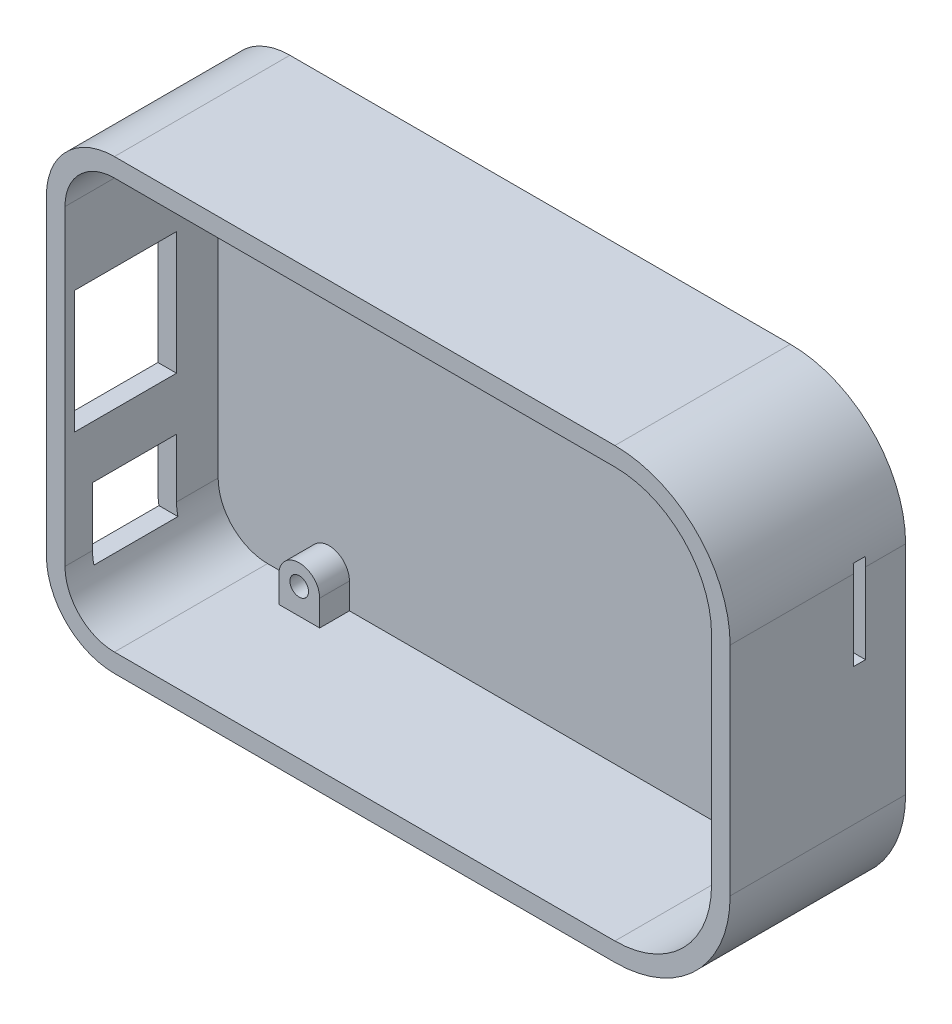
SolidWorks part; units mm, degrees
ref_plane "Front Plane" through (0, 0, 0) normal (0, 0, 1) x (1, 0, 0)
ref_plane "Top Plane" through (0, 0, 0) normal (0, 1, 0) x (1, 0, 0)
ref_plane "Right Plane" through (0, 0, 0) normal (1, 0, 0) x (0, 0, -1)
sketch "BeagleBone board" plane through (0, 0, 0) normal (0, 0, 1) x (1, 0, 0)
  line L1 (6.35, 0) -> (73.66, 0)
  line L2 (0, 6.35) -> (0, 48.26)
  line L3 (6.35, 54.61) -> (73.66, 54.61)
  line L4 (86.36, 12.7) -> (86.36, 41.91)
  line L5 (-2.5, 5) -> (12, 5)
  line L6 (-2.5, 5) -> (-2.5, 14)
  line L7 (-2.5, 14) -> (12, 14)
  line L8 (12, 5) -> (12, 14)
  line L9 (-2.5, 21.6) -> (19, 21.6)
  line L10 (-2.5, 21.6) -> (-2.5, 37.6)
  line L11 (-2.5, 37.6) -> (19, 37.6)
  line L12 (19, 21.6) -> (19, 37.6)
  arc A0 (6.35, 0) -> (0, 6.35) centre (6.35, 6.35) cw
  arc A1 (0, 48.26) -> (6.35, 54.61) centre (6.35, 48.26) cw
  arc A2 (73.66, 0) -> (86.36, 12.7) centre (73.66, 12.7) ccw
  arc A3 (73.66, 54.61) -> (86.36, 41.91) centre (73.66, 41.91) cw
  circle A4 centre (14.605, 51.435) radius 1.5
  circle A5 centre (14.605, 3.175) radius 1.5
  circle A6 centre (80.645, 48.26) radius 1.5
  circle A7 centre (80.645, 6.35) radius 1.5
  point P7 (0, 0)
  dimension "D3" = 6.35
  dimension "D4" = 12.7
  dimension "D5" = 3
  dimension "D1" = 86.36
  dimension "D2" = 54.61
  dimension "D6" = 3.175
  dimension "D7" = 14.605
  dimension "D8" = 51.435
  dimension "D9" = 6.35
  dimension "D10" = 48.26
  dimension "D11" = 80.645
  dimension "D12" = 2.5
  dimension "D13" = 16
  dimension "D14" = 21.5
  dimension "D15" = 9
  dimension "D16" = 14.5
  dimension "D17" = 5
  dimension "D18" = 21.6
sketch "Sketch5" plane through (0, 0, 0) normal (0, 0, 1) x (1, 0, 0)
  line L4 (73.66, 57.41) -> (6.35, 57.41)
  line L5 (-2.8, 48.26) -> (-2.8, 6.35)
  line L6 (6.35, -2.8) -> (73.66, -2.8)
  line L7 (89.16, 12.7) -> (89.16, 41.91)
  line L8 (73.66, 54.91) -> (6.35, 54.91)
  line L9 (86.66, 12.7) -> (86.66, 41.91)
  line L10 (6.35, -0.3) -> (73.66, -0.3)
  line L11 (-0.3, 48.26) -> (-0.3, 6.35)
  line L12 (73.66, 54.91) -> (17.355, 54.91)
  line L13 (86.66, 12.7) -> (86.66, 41.91)
  line L14 (6.35, -0.3) -> (11.855, -0.3)
  line L15 (-0.3, 48.26) -> (-0.3, 6.35)
  line L16 (17.355, 51.435) -> (17.355, 54.91)
  line L17 (11.855, 51.435) -> (11.855, 54.91)
  line L18 (77.895, 48.26) -> (77.895, 54.2008)
  line L19 (80.645, 45.51) -> (86.1516, 45.51)
  line L20 (77.895, 6.35) -> (77.895, 0.4092)
  line L21 (80.645, 9.1) -> (86.1516, 9.1)
  line L22 (11.855, 3.175) -> (11.855, -0.3)
  line L23 (17.355, -0.3) -> (73.66, -0.3)
  line L24 (6.35, -0.3) -> (73.66, -0.3) construction
  line L25 (17.355, 3.175) -> (17.355, -0.3)
  line L26 (11.855, 54.91) -> (6.35, 54.91)
  line L27 (73.66, 54.91) -> (6.35, 54.91) construction
  arc A4 (6.35, 57.41) -> (-2.8, 48.26) centre (6.35, 48.26) ccw
  arc A5 (-2.8, 6.35) -> (6.35, -2.8) centre (6.35, 6.35) ccw
  arc A6 (73.66, -2.8) -> (89.16, 12.7) centre (73.66, 12.7) ccw
  arc A7 (89.16, 41.91) -> (73.66, 57.41) centre (73.66, 41.91) ccw
  arc A8 (86.66, 41.91) -> (73.66, 54.91) centre (73.66, 41.91) ccw
  arc A9 (73.66, -0.3) -> (86.66, 12.7) centre (73.66, 12.7) ccw
  arc A10 (-0.3, 6.35) -> (6.35, -0.3) centre (6.35, 6.35) ccw
  arc A11 (6.35, 54.91) -> (-0.3, 48.26) centre (6.35, 48.26) ccw
  arc A12 (86.66, 41.91) -> (86.1516, 45.51) centre (73.66, 41.91) ccw
  arc A13 (73.66, -0.3) -> (77.895, 0.4092) centre (73.66, 12.7) ccw
  arc A14 (-0.3, 6.35) -> (6.35, -0.3) centre (6.35, 6.35) ccw
  arc A15 (6.35, 54.91) -> (-0.3, 48.26) centre (6.35, 48.26) ccw
  circle A16 centre (14.605, 51.435) radius 1.25
  arc A17 (11.855, 51.435) -> (17.355, 51.435) centre (14.605, 51.435) ccw
  circle A18 centre (80.645, 48.26) radius 1.25
  arc A19 (77.895, 48.26) -> (80.645, 45.51) centre (80.645, 48.26) ccw
  circle A20 centre (80.645, 6.35) radius 1.25
  arc A21 (80.645, 9.1) -> (77.895, 6.35) centre (80.645, 6.35) ccw
  circle A22 centre (14.605, 3.175) radius 1.25
  arc A23 (17.355, 3.175) -> (11.855, 3.175) centre (14.605, 3.175) ccw
  arc A24 (86.1516, 9.1) -> (86.66, 12.7) centre (73.66, 12.7) ccw
  arc A25 (73.66, -0.3) -> (86.66, 12.7) centre (73.66, 12.7) ccw construction
  arc A26 (77.895, 54.2008) -> (73.66, 54.91) centre (73.66, 41.91) ccw
  arc A27 (86.66, 41.91) -> (73.66, 54.91) centre (73.66, 41.91) ccw construction
  dimension "D3" = 2.5
  dimension "D4" = 5.5
  dimension "D1" = 0.3
  dimension "D2" = 2.5
extrude "Bottom frame" add sketch "Sketch5" along normal blind 4
sketch "Sketch6" plane through (0, 0, 4) normal (0, 0, 1) x (1, 0, 0)
  line L0 (-0.3, 48.26) -> (-0.3, 6.35) construction
  line L1 (-0.3, 48.26) -> (-0.3, 6.35)
  line L2 (86.66, 41.91) -> (86.66, 12.7)
  line L3 (73.66, 54.91) -> (6.35, 54.91)
  line L4 (73.66, 57.41) -> (6.35, 57.41)
  line L5 (-2.8, 48.26) -> (-2.8, 6.35)
  line L6 (6.35, -2.8) -> (73.66, -2.8)
  line L7 (89.16, 12.7) -> (89.16, 41.91)
  line L8 (73.66, 57.41) -> (6.35, 57.41)
  line L9 (-2.8, 48.26) -> (-2.8, 6.35)
  line L10 (6.35, -2.8) -> (73.66, -2.8)
  line L11 (89.16, 12.7) -> (89.16, 41.91)
  line L12 (6.35, -0.3) -> (73.66, -0.3)
  arc A0 (6.35, 54.91) -> (-0.3, 48.26) centre (6.35, 48.26) ccw construction
  arc A1 (-0.3, 6.35) -> (6.35, -0.3) centre (6.35, 6.35) ccw construction
  arc A2 (6.35, 54.91) -> (-0.3, 48.26) centre (6.35, 48.26) ccw
  arc A3 (-0.3, 6.35) -> (6.35, -0.3) centre (6.35, 6.35) ccw
  arc A4 (89.16, 41.91) -> (73.66, 57.41) centre (73.66, 41.91) ccw
  arc A5 (6.35, 57.41) -> (-2.8, 48.26) centre (6.35, 48.26) ccw
  arc A6 (-2.8, 6.35) -> (6.35, -2.8) centre (6.35, 6.35) ccw
  arc A7 (73.66, -2.8) -> (89.16, 12.7) centre (73.66, 12.7) ccw
  arc A8 (89.16, 41.91) -> (73.66, 57.41) centre (73.66, 41.91) ccw
  arc A9 (6.35, 57.41) -> (-2.8, 48.26) centre (6.35, 48.26) ccw
  arc A10 (-2.8, 6.35) -> (6.35, -2.8) centre (6.35, 6.35) ccw
  arc A11 (73.66, -2.8) -> (89.16, 12.7) centre (73.66, 12.7) ccw
  arc A12 (86.66, 41.91) -> (73.66, 54.91) centre (73.66, 41.91) ccw
  arc A13 (77.895, 54.2008) -> (73.66, 54.91) centre (73.66, 41.91) ccw construction
  arc A14 (73.66, -0.3) -> (86.66, 12.7) centre (73.66, 12.7) ccw
  arc A15 (86.1516, 9.1) -> (86.66, 12.7) centre (73.66, 12.7) ccw construction
  dimension "D1" = 0
extrude "PCB" add sketch "Sketch6" along normal blind 1.6
sketch "Sketch7" plane through (0, 0, 5.6) normal (0, 0, 1) x (1, 0, 0)
  line L0 (73.66, 54.91) -> (6.35, 54.91) construction
  line L1 (73.66, 54.91) -> (6.35, 54.91)
  line L2 (-0.3, 48.26) -> (-0.3, 6.35) construction
  line L3 (-0.3, 48.26) -> (-0.3, 37.85)
  line L4 (73.66, 57.41) -> (6.35, 57.41)
  line L5 (-2.8, 48.26) -> (-2.8, 6.35)
  line L6 (6.35, -2.8) -> (73.66, -2.8)
  line L7 (89.16, 12.7) -> (89.16, 41.91)
  line L8 (73.66, 57.41) -> (6.35, 57.41)
  line L9 (-2.8, 48.26) -> (-2.8, 37.85)
  line L10 (6.35, -2.8) -> (73.66, -2.8)
  line L11 (89.16, 12.7) -> (89.16, 41.91)
  line L12 (6.35, -0.3) -> (73.66, -0.3) construction
  line L13 (6.35, -0.3) -> (73.66, -0.3)
  line L14 (86.66, 12.7) -> (86.66, 41.91) construction
  line L15 (86.66, 12.7) -> (86.66, 41.91)
  line L16 (-0.3, 21.35) -> (-2.8, 21.35)
  line L17 (-2.8, 37.85) -> (-0.3, 37.85)
  line L18 (-0.3, 21.35) -> (-0.3, 14.25)
  line L19 (-2.8, 21.35) -> (-2.8, 14.25)
  line L20 (-2.5, 21.6) -> (19, 21.6) construction
  line L21 (-2.5, 37.6) -> (19, 37.6) construction
  line L22 (-2.659, 4.75) -> (-0.1046, 4.75)
  line L23 (-0.3, 14.25) -> (-2.8, 14.25)
  line L24 (-2.5, 5) -> (12, 5) construction
  line L25 (-2.5, 14) -> (12, 14) construction
  arc A0 (6.35, 54.61) -> (0, 48.26) centre (6.35, 48.26) ccw construction
  arc A1 (6.35, 54.61) -> (0, 48.26) centre (6.35, 48.26) ccw
  arc A2 (6.35, 54.91) -> (-0.3, 48.26) centre (6.35, 48.26) ccw construction
  arc A3 (6.35, 54.91) -> (-0.3, 48.26) centre (6.35, 48.26) ccw
  arc A4 (89.16, 41.91) -> (73.66, 57.41) centre (73.66, 41.91) ccw
  arc A5 (6.35, 57.41) -> (-2.8, 48.26) centre (6.35, 48.26) ccw
  arc A6 (-2.8, 6.35) -> (6.35, -2.8) centre (6.35, 6.35) ccw
  arc A7 (73.66, -2.8) -> (89.16, 12.7) centre (73.66, 12.7) ccw
  arc A8 (89.16, 41.91) -> (73.66, 57.41) centre (73.66, 41.91) ccw
  arc A9 (6.35, 57.41) -> (-2.8, 48.26) centre (6.35, 48.26) ccw
  arc A10 (-2.659, 4.75) -> (6.35, -2.8) centre (6.35, 6.35) ccw
  arc A11 (73.66, -2.8) -> (89.16, 12.7) centre (73.66, 12.7) ccw
  arc A12 (-0.3, 6.35) -> (6.35, -0.3) centre (6.35, 6.35) ccw construction
  arc A13 (-0.1046, 4.75) -> (6.35, -0.3) centre (6.35, 6.35) ccw
  arc A14 (73.66, -0.3) -> (86.66, 12.7) centre (73.66, 12.7) ccw construction
  arc A15 (73.66, -0.3) -> (86.66, 12.7) centre (73.66, 12.7) ccw
  arc A16 (86.66, 41.91) -> (73.66, 54.91) centre (73.66, 41.91) ccw construction
  arc A17 (86.66, 41.91) -> (73.66, 54.91) centre (73.66, 41.91) ccw
  arc M9 (89.16, 41.91) -> (73.66, 57.41) centre (73.66, 41.91) ccw
  line M10 (73.66, 57.41) -> (6.35, 57.41)
  arc M11 (6.35, 57.41) -> (-2.8, 48.26) centre (6.35, 48.26) ccw
  line M12 (-2.8, 48.26) -> (-2.8, 6.35)
  arc M13 (-2.8, 6.35) -> (6.35, -2.8) centre (6.35, 6.35) ccw
  line M14 (6.35, -2.8) -> (73.66, -2.8)
  arc M15 (73.66, -2.8) -> (89.16, 12.7) centre (73.66, 12.7) ccw
  line M16 (89.16, 12.7) -> (89.16, 41.91)
  line M17 (6.35, 54.91) -> (73.66, 54.91)
  arc M18 (73.66, 54.91) -> (86.66, 41.91) centre (73.66, 41.91) cw
  line M19 (86.66, 41.91) -> (86.66, 12.7)
  arc M20 (86.66, 12.7) -> (73.66, -0.3) centre (73.66, 12.7) cw
  line M21 (73.66, -0.3) -> (6.35, -0.3)
  arc M22 (6.35, -0.3) -> (-0.3, 6.35) centre (6.35, 6.35) cw
  line M23 (-0.3, 6.35) -> (-0.3, 48.26)
  arc M24 (-0.3, 48.26) -> (6.35, 54.91) centre (6.35, 48.26) cw
  dimension "D2" = 0.25
  dimension "D3" = 0.25
  dimension "D4" = 0.25
  dimension "D5" = 0.25
  dimension "D1" = 0
extrude "upper frame" add sketch "Sketch7" along normal blind 15 contours L22 L17 M13 M14 M15 M16 M9 M10 M11 M12 M23 M24 M17 M18 M19 M20 M21 M22 | L23 L16 M23 M12
sketch "Sketch8" plane through (0, 0, 0) normal (0, 0, -1) x (-1, 0, 0)
  line L4 (-89.16, 41.91) -> (-89.16, 12.7)
  line L5 (-73.66, -2.8) -> (-6.35, -2.8)
  line L6 (2.8, 6.35) -> (2.8, 48.26)
  line L7 (-6.35, 57.41) -> (-73.66, 57.41)
  line L8 (-89.16, 41.91) -> (-89.16, 12.7)
  line L9 (-73.66, -2.8) -> (-6.35, -2.8)
  line L10 (2.8, 6.35) -> (2.8, 48.26)
  line L11 (-6.35, 57.41) -> (-73.66, 57.41)
  arc A4 (-73.66, 57.41) -> (-89.16, 41.91) centre (-73.66, 41.91) ccw
  arc A5 (-89.16, 12.7) -> (-73.66, -2.8) centre (-73.66, 12.7) ccw
  arc A6 (-6.35, -2.8) -> (2.8, 6.35) centre (-6.35, 6.35) ccw
  arc A7 (2.8, 48.26) -> (-6.35, 57.41) centre (-6.35, 48.26) ccw
  arc A8 (-73.66, 57.41) -> (-89.16, 41.91) centre (-73.66, 41.91) ccw
  arc A9 (-89.16, 12.7) -> (-73.66, -2.8) centre (-73.66, 12.7) ccw
  arc A10 (-6.35, -2.8) -> (2.8, 6.35) centre (-6.35, 6.35) ccw
  arc A11 (2.8, 48.26) -> (-6.35, 57.41) centre (-6.35, 48.26) ccw
  dimension "D1" = 0
extrude "bottom" add sketch "Sketch8" along normal blind 3
sketch "Sketch9" plane through (0, 0, 20.6) normal (0, 0, 1) x (1, 0, 0)
  line L1 (-2.8, 37.85) -> (-0.3, 37.85)
  line L2 (-2.8, 37.85) -> (-2.8, 21.35)
  line L3 (-2.8, 21.35) -> (-0.3, 21.35)
  line L4 (-0.3, 37.85) -> (-0.3, 21.35)
extrude "network connector boss" add sketch "Sketch9" against normal offset from surface (1.3 mm away) 13.7 up to face at (-1.8625, 33.725, 5.6)
sketch "Sketch10" plane through (0, 0, 20.6) normal (0, 0, 1) x (1, 0, 0)
  line L0 (-0.3, 14.25) -> (-2.8, 14.25) construction
  line L1 (-2.8, 14.25) -> (-2.8, 6.35) construction
  line L2 (-0.3, 14.25) -> (-2.8, 14.25)
  line L3 (-2.8, 14.25) -> (-2.8, 6.35)
  line L4 (-2.659, 4.75) -> (-0.1046, 4.75) construction
  line L5 (-2.659, 4.75) -> (-0.1046, 4.75)
  line L6 (-0.3, 48.26) -> (-0.3, 6.35) construction
  line L7 (-0.3, 14.25) -> (-0.3, 6.35)
  arc A0 (-2.8, 6.35) -> (-2.659, 4.75) centre (6.35, 6.35) ccw construction
  arc A1 (-2.8, 6.35) -> (-2.659, 4.75) centre (6.35, 6.35) ccw
  arc A2 (-0.3, 6.35) -> (-0.1046, 4.75) centre (6.35, 6.35) ccw construction
  arc A3 (-0.3, 6.35) -> (-0.1046, 4.75) centre (6.35, 6.35) ccw
extrude "Boss-Extrude8" add sketch "Sketch10" against normal offset from surface (3.7 mm away) 11.3 up to face at (-1.7348, 10.0333, 5.6)
sketch "Sketch11" plane through (-2.8, 0, 0) normal (-1, 0, 0) x (0, 0, 1)
  line L0 (4, 51.435) -> (4, 54.91) construction
  line L1 (0.1, 48.06) -> (4, 48.06)
  line L2 (0.1, 48.06) -> (0.1, 40.36)
  line L3 (0.1, 40.36) -> (4, 40.36)
  line L4 (4, 48.06) -> (4, 40.36)
  point P6 (0, 54.61)
  dimension "D1" = 3.9
  dimension "D2" = 7.7
  dimension "D3" = 6.55
extrude "mini-USB" cut sketch "Sketch11" against normal up to next
sketch "Sketch12" plane through (89.16, 0, 0) normal (1, 0, 0) x (0, 0, -1)
  line L0 (-4, 40.36) -> (-4, 48.06) construction
  line L1 (-4, 43.11) -> (-2.39, 43.11)
  line L2 (-4, 43.11) -> (-4, 31.11)
  line L3 (-4, 31.11) -> (-2.39, 31.11)
  line L4 (-2.39, 43.11) -> (-2.39, 31.11)
  point P0 (0, 54.61)
  dimension "D1" = 12
  dimension "D2" = 1.61
  dimension "D3" = 11.5
extrude "Cut-Extrude3" cut sketch "Sketch12" against normal up to next
sketch "Sketch13" [suppressed] plane through (0, 0, 0) normal (0, 0, 1) x (1, 0, 0)
  line L4 (73.66, 57.41) -> (6.35, 57.41)
  line L5 (-2.8, 48.26) -> (-2.8, 6.35)
  line L6 (6.35, -2.8) -> (73.66, -2.8)
  line L7 (89.16, 12.7) -> (89.16, 41.91)
  line L8 (73.66, 54.91) -> (6.35, 54.91)
  line L9 (86.66, 12.7) -> (86.66, 41.91)
  line L10 (6.35, -0.3) -> (73.66, -0.3)
  line L11 (-0.3, 48.26) -> (-0.3, 6.35)
  line L12 (73.66, 54.91) -> (6.35, 54.91) construction
  line L13 (86.66, 12.7) -> (86.66, 41.91) construction
  line L14 (6.35, -0.3) -> (73.66, -0.3) construction
  line L15 (-0.3, 48.26) -> (-0.3, 6.35) construction
  circle A1 centre (14.605, 51.435) radius 1.5 construction
  circle A2 centre (80.645, 48.26) radius 1.5 construction
  circle A3 centre (80.645, 6.35) radius 1.5 construction
  arc A4 (6.35, 57.41) -> (-2.8, 48.26) centre (6.35, 48.26) ccw
  arc A5 (-2.8, 6.35) -> (6.35, -2.8) centre (6.35, 6.35) ccw
  arc A6 (73.66, -2.8) -> (89.16, 12.7) centre (73.66, 12.7) ccw
  arc A7 (89.16, 41.91) -> (73.66, 57.41) centre (73.66, 41.91) ccw
  arc A8 (86.66, 41.91) -> (73.66, 54.91) centre (73.66, 41.91) ccw
  arc A9 (73.66, -0.3) -> (86.66, 12.7) centre (73.66, 12.7) ccw
  arc A10 (-0.3, 6.35) -> (6.35, -0.3) centre (6.35, 6.35) ccw
  arc A11 (6.35, 54.91) -> (-0.3, 48.26) centre (6.35, 48.26) ccw
  arc A12 (86.66, 41.91) -> (73.66, 54.91) centre (73.66, 41.91) ccw construction
  arc A13 (73.66, -0.3) -> (86.66, 12.7) centre (73.66, 12.7) ccw construction
  arc A14 (-0.3, 6.35) -> (6.35, -0.3) centre (6.35, 6.35) ccw construction
  arc A15 (6.35, 54.91) -> (-0.3, 48.26) centre (6.35, 48.26) ccw construction
  circle A18 centre (14.605, 3.175) radius 1.5 construction
  circle A19 centre (14.605, 51.435) radius 1.5
  circle A20 centre (80.645, 48.26) radius 1.5
  circle A21 centre (80.645, 6.35) radius 1.5
  circle A22 centre (14.605, 3.175) radius 1.5
  dimension "D1" = 0.3
  dimension "D2" = 2.5
extrude "Boss-Extrude9" [suppressed] add sketch "Sketch13" along normal blind 2
sketch "Sketch14" [suppressed] plane through (0, 0, 0) normal (0, 0, -1) x (-1, 0, 0)
  line L0 (-6.35, 54.61) -> (-73.66, 54.61) construction
  line L1 (-86.36, 12.7) -> (-86.36, 41.91) construction
  line L2 (-6.35, 0) -> (-73.66, 0) construction
  line L3 (0, 6.35) -> (0, 48.26) construction
  line L4 (-6.35, 54.61) -> (-73.66, 54.61)
  line L5 (-86.36, 12.7) -> (-86.36, 41.91)
  line L6 (-6.35, 0) -> (-73.66, 0)
  line L7 (0, 6.35) -> (0, 48.26)
  arc A0 (-73.66, 54.61) -> (-86.36, 41.91) centre (-73.66, 41.91) ccw construction
  arc A1 (-86.36, 12.7) -> (-73.66, 0) centre (-73.66, 12.7) ccw construction
  arc A2 (-6.35, 0) -> (0, 6.35) centre (-6.35, 6.35) ccw construction
  arc A3 (0, 48.26) -> (-6.35, 54.61) centre (-6.35, 48.26) ccw construction
  arc A4 (-73.66, 54.61) -> (-86.36, 41.91) centre (-73.66, 41.91) ccw
  arc A5 (-86.36, 12.7) -> (-73.66, 0) centre (-73.66, 12.7) ccw
  arc A6 (-6.35, 0) -> (0, 6.35) centre (-6.35, 6.35) ccw
  arc A7 (0, 48.26) -> (-6.35, 54.61) centre (-6.35, 48.26) ccw
  circle A12 centre (-80.645, 48.26) radius 3.15
  circle A13 centre (-14.605, 51.435) radius 3.15
  circle A14 centre (-14.605, 3.175) radius 3.15
  circle A15 centre (-80.645, 6.35) radius 3.15
  dimension "D1" = 6.3
extrude "Boss-Extrude10" [suppressed] add sketch "Sketch14" along normal blind 1
sketch "Sketch15" [suppressed] plane through (0, 0, 2) normal (0, 0, 1) x (1, 0, 0)
  line L0 (73.66, 57.41) -> (6.35, 57.41) construction
  line L1 (18.2, 5.75) -> (77.7, 5.75)
  line L2 (18.2, 5.75) -> (18.2, -0.25)
  line L3 (18.2, -0.25) -> (77.7, -0.25)
  line L4 (77.7, 5.75) -> (77.7, -0.25)
  line L5 (18.2, 48.86) -> (77.7, 48.86)
  line L6 (18.2, 48.86) -> (18.2, 54.86)
  line L7 (18.2, 54.86) -> (77.7, 54.86)
  line L8 (77.7, 48.86) -> (77.7, 54.86)
  line L9 (6.35, -2.8) -> (73.66, -2.8) construction
  line L10 (-2.8, 48.26) -> (-2.8, 6.35) construction
  dimension "D1" = 2.55
  dimension "D2" = 2.55
  dimension "D3" = 6
  dimension "D4" = 6
  dimension "D5" = 59.5
  dimension "D6" = 21
extrude "Cut-Extrude4" [suppressed] cut sketch "Sketch15" against normal through all
